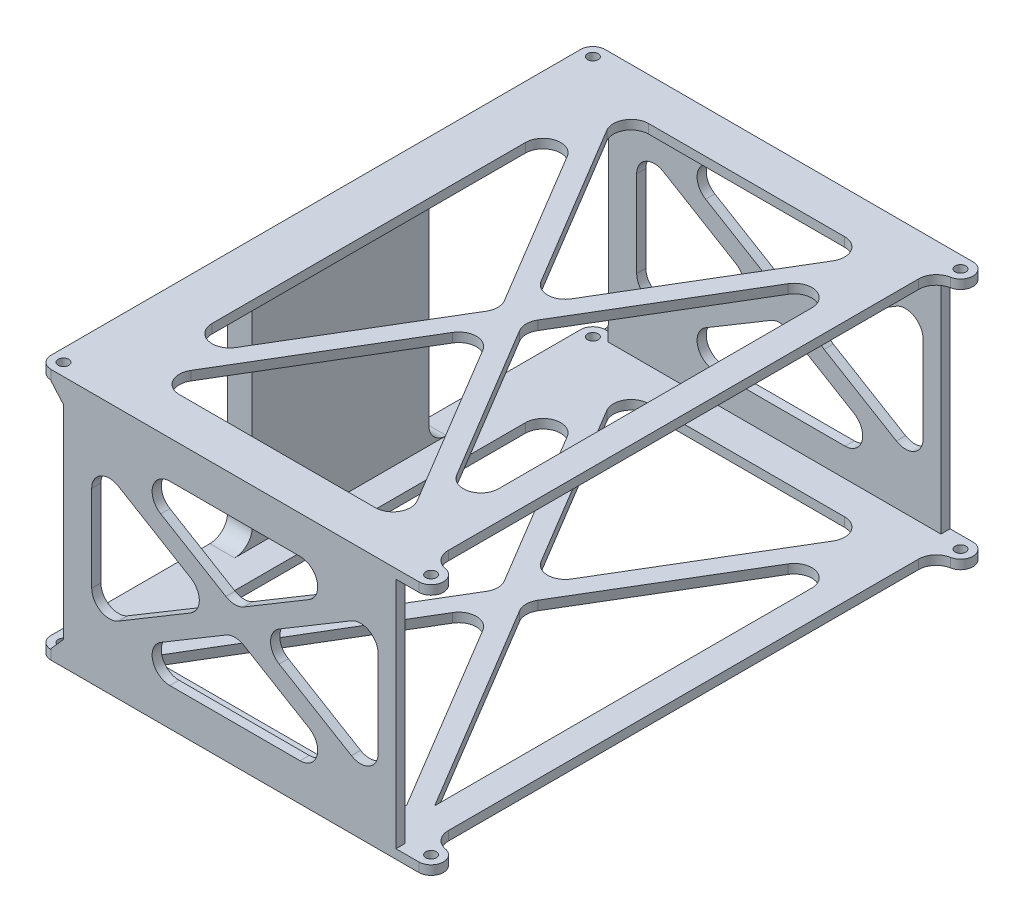
SolidWorks part; units mm, degrees
ref_plane "Front Plane" through (0, 0, 0) normal (0, 0, 1) x (1, 0, 0)
ref_plane "Top Plane" through (0, 0, 0) normal (0, 1, 0) x (1, 0, 0)
ref_plane "Right Plane" through (0, 0, 0) normal (1, 0, 0) x (0, 0, -1)
sketch "Sketch3" plane through (0, 0, 0) normal (0, 1, 0) x (1, 0, 0)
  line L24 (-48.55, 78.45) -> (49.2, 78.45)
  line L34 (-52.05, 0) -> (52.05, 0) construction
  line L37 (49.2, 78.45) -> (55.55, 78.45)
  line L41 (-48.55, -78.45) -> (49.2, -78.45)
  line L43 (52.05, 71.45) -> (55.55, 71.45)
  line L44 (52.05, -71.45) -> (55.55, -71.45)
  line L45 (49.2, -78.45) -> (55.55, -78.45)
  line L46 (52.05, -71.45) -> (52.05, 71.45)
  line L47 (-52.05, 74.95) -> (-52.05, -74.95)
  arc A8 (-48.55, 78.45) -> (-52.05, 74.95) centre (-48.55, 74.95) ccw
  circle A12 centre (-48.55, 74.95) radius 1.5
  arc A15 (55.55, 78.45) -> (55.55, 71.45) centre (55.55, 74.95) cw
  circle A19 centre (-48.55, -74.95) radius 1.5
  arc A21 (-48.55, -78.45) -> (-52.05, -74.95) centre (-48.55, -74.95) cw
  circle A22 centre (55.55, 74.95) radius 1.5
  circle A23 centre (55.55, -74.95) radius 1.5
  arc A24 (55.55, -78.45) -> (55.55, -71.45) centre (55.55, -74.95) ccw
  point P13 (0, 0)
  dimension "D3" = 7
  dimension "D4" = 3
  dimension "D5" = 6.35
  dimension "D6" = 3.5
  dimension "D1" = 156.9
  dimension "D2" = 101.25
extrude "Boss-Extrude2" add sketch "Sketch3" along normal blind 71.3
sketch "Sketch10" plane through (0, 0, -78.45) normal (0, 0, -1) x (-1, 0, 0)
  line L1 (52.05, 71.3) -> (48.55, 71.3) construction
  line L8 (-55.55, 0) -> (48.55, 0) construction
  line L9 (-55.55, 71.3) -> (48.55, 71.3) construction
  line L11 (-3.5, 71.3) -> (-3.5, 0) construction
  line L20 (52.05, 68.7) -> (48.55, 68.7)
  line L21 (48.55, 68.7) -> (48.55, 68.45)
  line L22 (48.55, 68.45) -> (45.05, 64.45)
  line L23 (45.05, 64.45) -> (45.05, 6.85)
  line L24 (45.05, 6.85) -> (48.55, 2.85)
  line L25 (48.55, 2.85) -> (48.55, 2.6)
  line L26 (48.55, 2.6) -> (52.05, 2.6)
  line L27 (52.05, 68.7) -> (52.05, 2.6)
  line L28 (48.55, 0) -> (52.05, 0) construction
  line L29 (52.05, 71.3) -> (52.05, 0) construction
  line L30 (-59.05, 71.3) -> (-59.05, 0) construction
  line L31 (-59.05, 68.7) -> (-49.1, 68.7)
  line L32 (-59.05, 68.7) -> (-59.05, 2.6)
  line L33 (-59.05, 2.6) -> (-49.1, 2.6)
  line L34 (-49.1, 68.7) -> (-49.1, 2.6)
  dimension "D1" = 7
  dimension "D2" = 9.95
  dimension "D3" = 2.6
  dimension "D4" = 2.6
  dimension "D5" = 3.5
  dimension "D6" = 0.25
  dimension "D7" = 4
  dimension "D8" = 4
  dimension "D9" = 0.25
  dimension "D10" = 3.5
  dimension "D11" = 57.6
extrude "Cut-Extrude7" cut sketch "Sketch10" against normal through all
sketch "Sketch14" plane through (-52.05, 0, 0) normal (-1, 0, 0) x (0, 0, 1)
  line L0 (74.95, 68.7) -> (-74.95, 68.7) construction
  line L1 (-25, 68.7) -> (25, 68.7)
  line L2 (-25, 68.7) -> (-25, 2.6)
  line L3 (-25, 2.6) -> (25, 2.6)
  line L4 (25, 68.7) -> (25, 2.6)
  line L5 (74.95, 2.6) -> (-74.95, 2.6) construction
  line L6 (-78.45, 64.45) -> (-78.45, 6.85) construction
  line L7 (78.45, 64.45) -> (78.45, 6.85) construction
  dimension "D1" = 53.45
  dimension "D2" = 53.45
extrude "Boss-Extrude4" add sketch "Sketch14" against normal up to next
sketch "Sketch8" plane through (52.05, 0, 0) normal (1, 0, 0) x (0, 0, -1)
  line L1 (-75.85, 2.6) -> (75.85, 2.6)
  line L2 (-75.85, 2.6) -> (-75.85, 68.7)
  line L3 (-75.85, 68.7) -> (75.85, 68.7)
  line L4 (75.85, 2.6) -> (75.85, 68.7)
  line L5 (-75.85, 2.6) -> (75.85, 68.7) construction
  line L6 (-75.85, 68.7) -> (75.85, 2.6) construction
  line L8 (-78.45, 2.6) -> (-78.45, 68.7) construction
  line L9 (78.45, 2.6) -> (78.45, 68.7) construction
  line L12 (-71.45, 71.3) -> (71.45, 71.3) construction
  line L13 (-71.45, 0) -> (71.45, 0) construction
  point P0 (0, 35.65)
  dimension "D1" = 2.6
  dimension "D2" = 2.6
  dimension "D3" = 2.6
  dimension "D4" = 2.6
extrude "Cut-Extrude5" cut sketch "Sketch8" against normal up to surface (97.1 mm away) and the other way through all up to face at (-45.05, 35.65, 51.725)
sketch "Sketch15" plane through (0, 2.6, 0) normal (0, 1, 0) x (1, 0, 0)
  line L0 (-48.55, 71.45) -> (-52.05, 71.45)
  line L1 (-52.05, 74.95) -> (-52.05, -74.95) construction
  line L2 (-52.05, 71.45) -> (-52.05, 74.95)
  line L4 (-48.55, -71.45) -> (-52.05, -71.45)
  line L5 (-52.05, -71.45) -> (-52.05, -74.95)
  line L6 (54.65, -71.45) -> (54.65, -78.45)
  line L16 (54.65, -78.45) -> (55.55, -78.45)
  line L17 (54.65, -71.45) -> (55.55, -71.45)
  line L18 (55.55, 71.45) -> (54.65, 71.45)
  line L19 (54.65, 71.45) -> (54.65, 78.45)
  line L21 (54.65, 78.45) -> (55.55, 78.45)
  arc A4 (-48.55, 71.45) -> (-52.05, 74.95) centre (-48.55, 74.95) ccw
  arc A5 (-52.05, -74.95) -> (-48.55, -71.45) centre (-48.55, -74.95) ccw
  arc A6 (-48.55, -71.45) -> (-52.05, -74.95) centre (-48.55, -74.95) ccw construction
  arc A7 (-52.05, 74.95) -> (-48.55, 71.45) centre (-48.55, 74.95) ccw construction
  arc A11 (55.55, 78.45) -> (55.55, 71.45) centre (55.55, 74.95) cw
  arc A12 (55.55, -71.45) -> (55.55, -78.45) centre (55.55, -74.95) cw
  dimension "D1" = 2.6
sketch "Sketch16" plane through (-45.05, 0, 0) normal (1, 0, 0) x (0, 0, -1)
  line L70 (-71.45, 2.6) -> (-78.45, 2.6) construction
  line L87 (-25, 64.45) -> (-75.85, 64.45)
  line L88 (-25, 64.45) -> (-25, 68.7)
  line L89 (-25, 68.7) -> (-75.85, 68.7)
  line L90 (-75.85, 64.45) -> (-75.85, 68.7)
  line L91 (25, 64.45) -> (75.85, 64.45)
  line L92 (25, 64.45) -> (25, 68.7)
  line L93 (25, 68.7) -> (75.85, 68.7)
  line L94 (75.85, 64.45) -> (75.85, 68.7)
  line L95 (25, 6.85) -> (75.85, 6.85)
  line L96 (25, 6.85) -> (25, 2.6)
  line L97 (25, 2.6) -> (75.85, 2.6)
  line L98 (75.85, 6.85) -> (75.85, 2.6)
  line L99 (-25, 6.85) -> (-75.85, 6.85)
  line L100 (-25, 6.85) -> (-25, 2.6)
  line L101 (-25, 2.6) -> (-75.85, 2.6)
  line L102 (-75.85, 6.85) -> (-75.85, 2.6)
  line L103 (75.85, 2.6) -> (-75.85, 2.6) construction
extrude "Cut-Extrude10" cut sketch "Sketch16" against normal through all
extrude "Cut-Extrude11" cut sketch "Sketch15" against normal up to surface (66.1 mm away) from surface at 66.1 up to face at (55.55, 2.6, -76.45) starting at face at (55.55, 68.7, -73.45)
sketch "Sketch18" plane through (0, 0, 78.45) normal (0, 0, 1) x (1, 0, 0)
  line L1 (-45.05, 68.7) -> (52.05, 68.7) construction
  line L2 (-45.05, 68.7) -> (-45.05, 2.6) construction
  line L3 (-45.05, 2.6) -> (52.05, 2.6) construction
  line L4 (52.05, 68.7) -> (52.05, 2.6) construction
  line L6 (-45.05, 2.6) -> (-45.05, 68.7) construction
  line L7 (-37.05, 56.7) -> (-1.8449, 35.65)
  line L8 (-33.05, 60.7) -> (40.05, 60.7)
  line L9 (-37.05, 56.7) -> (-37.05, 14.6)
  line L10 (-33.05, 10.6) -> (40.05, 10.6)
  line L11 (44.05, 56.7) -> (44.05, 14.6)
  line L12 (-1.8449, 35.65) -> (-37.05, 14.6)
  line L13 (-33.05, 60.7) -> (3.5, 38.8458)
  line L14 (3.5, 38.8458) -> (40.05, 60.7)
  line L15 (-33.05, 10.6) -> (3.5, 32.4542)
  line L16 (3.5, 32.4542) -> (40.05, 10.6)
  line L17 (44.05, 56.7) -> (8.8449, 35.65)
  line L18 (8.8449, 35.65) -> (44.05, 14.6)
  line L19 (-37.05, 60.7) -> (-37.05, 56.7) construction
  line L20 (-37.05, 60.7) -> (-33.05, 60.7) construction
  line L21 (40.05, 60.7) -> (44.05, 60.7) construction
  line L22 (44.05, 60.7) -> (44.05, 56.7) construction
  line L23 (40.05, 10.6) -> (44.05, 10.6) construction
  line L24 (44.05, 14.6) -> (44.05, 10.6) construction
  line L25 (-37.05, 14.6) -> (-37.05, 10.6) construction
  line L26 (-37.05, 10.6) -> (-33.05, 10.6) construction
  line L27 (49.1, 68.7) -> (55.55, 68.7) construction
  line L28 (49.1, 2.6) -> (49.1, 68.7) construction
  line L29 (-48.55, 0) -> (55.55, 0) construction
  dimension "D1" = 8
  dimension "D2" = 8
  dimension "D3" = 8
  dimension "D4" = 8
  dimension "D5" = 4
  dimension "D6" = 4
  dimension "D7" = 4
  dimension "D8" = 4
  dimension "D9" = 2.95
  dimension "D10" = 2.6
extrude "Cut-Extrude12" cut sketch "Sketch18" against normal through all
sketch "Sketch19" plane through (0, 71.3, 0) normal (0, 1, 0) x (1, 0, 0)
  line L0 (-37.05, 62.45) -> (0.3037, 0)
  line L1 (-45.05, 78.45) -> (52.05, 78.45) construction
  line L2 (-45.05, 78.45) -> (-45.05, -78.45) construction
  line L3 (-45.05, -78.45) -> (52.05, -78.45) construction
  line L4 (52.05, 78.45) -> (52.05, -78.45) construction
  line L5 (-33.05, 66.45) -> (40.05, 66.45)
  line L6 (-37.05, 62.45) -> (-37.05, -62.45)
  line L7 (-33.05, -66.45) -> (40.05, -66.45)
  line L8 (44.05, 62.45) -> (44.05, -62.45)
  line L9 (0.3037, 0) -> (-37.05, -62.45)
  line L10 (-33.05, 66.45) -> (3.5, 5.3437)
  line L11 (3.5, 5.3437) -> (40.05, 66.45)
  line L12 (44.05, 62.45) -> (6.6963, 0)
  line L13 (6.6963, 0) -> (44.05, -62.45)
  line L14 (-33.05, -66.45) -> (3.5, -5.3437)
  line L15 (3.5, -5.3437) -> (40.05, -66.45)
  line L16 (-37.05, 66.45) -> (-37.05, 62.45) construction
  line L17 (-37.05, 66.45) -> (-33.05, 66.45) construction
  line L18 (40.05, 66.45) -> (44.05, 66.45) construction
  line L19 (44.05, 66.45) -> (44.05, 62.45) construction
  line L20 (40.05, -66.45) -> (44.05, -66.45) construction
  line L21 (44.05, -62.45) -> (44.05, -66.45) construction
  line L22 (-37.05, -62.45) -> (-37.05, -66.45) construction
  line L23 (-37.05, -66.45) -> (-33.05, -66.45) construction
  line L24 (-52.05, 74.95) -> (-52.05, -74.95) construction
  line L25 (55.55, 78.45) -> (-48.55, 78.45) construction
  line L27 (52.05, -71.45) -> (52.05, 71.45) construction
  line L28 (-48.55, -78.45) -> (55.55, -78.45) construction
  dimension "D1" = 12
  dimension "D2" = 8
  dimension "D3" = 8
  dimension "D4" = 12
  dimension "D5" = 4
  dimension "D6" = 4
  dimension "D7" = 4
  dimension "D8" = 4
  dimension "D9" = 4
  dimension "D10" = 4
  dimension "D11" = 4
  dimension "D12" = 7
extrude "Cut-Extrude13" cut sketch "Sketch19" against normal through all
fillet "Fillet1" radius 5 52 edges at (-33.05, 60.7, 77.15) (-37.05, 56.7, 77.15) (44.05, 56.7, 77.15) (40.05, 60.7, 77.15) (40.05, 10.6, 77.15) (44.05, 14.6, 77.15) (-37.05, 14.6, 77.15) (-33.05, 10.6, 77.15) (-37.05, 56.7, -77.15) (-33.05, 60.7, -77.15) (40.05, 60.7, -77.15) (44.05, 56.7, -77.15) (40.05, 10.6, -77.15) (44.05, 14.6, -77.15) (-37.05, 14.6, -77.15) (-33.05, 10.6, -77.15) (3.5, 32.4542, -77.15) (-1.8449, 35.65, -77.15) (3.5, 38.8458, -77.15) (8.8449, 35.65, -77.15) (3.5, 32.4542, 77.15) (-1.8449, 35.65, 77.15) (3.5, 38.8458, 77.15) (8.8449, 35.65, 77.15) (52.05, 1.3, -71.45) (52.05, 70, -71.45) (52.05, 70, 71.45) (52.05, 1.3, 71.45) (-37.05, 1.3, -62.45) (-33.05, 1.3, -66.45) (44.05, 1.3, -62.45) (40.05, 1.3, -66.45) (3.5, 1.3, -5.3437) (0.3037, 1.3, 0) (3.5, 1.3, 5.3437) (6.6963, 1.3, 0) (-37.05, 70, -62.45) (-33.05, 70, -66.45) (-37.05, 70, 62.45) (-33.05, 70, 66.45) (40.05, 70, 66.45) (44.05, 70, 62.45) (44.05, 70, -62.45) (40.05, 70, -66.45) (0.3037, 70, 0) (3.5, 70, -5.3437) (6.6963, 70, 0) (3.5, 70, 5.3437) (-48.55, 68.7, -25) (-48.55, 2.6, -25) (-48.55, 2.6, 25) (-48.55, 68.7, 25)
